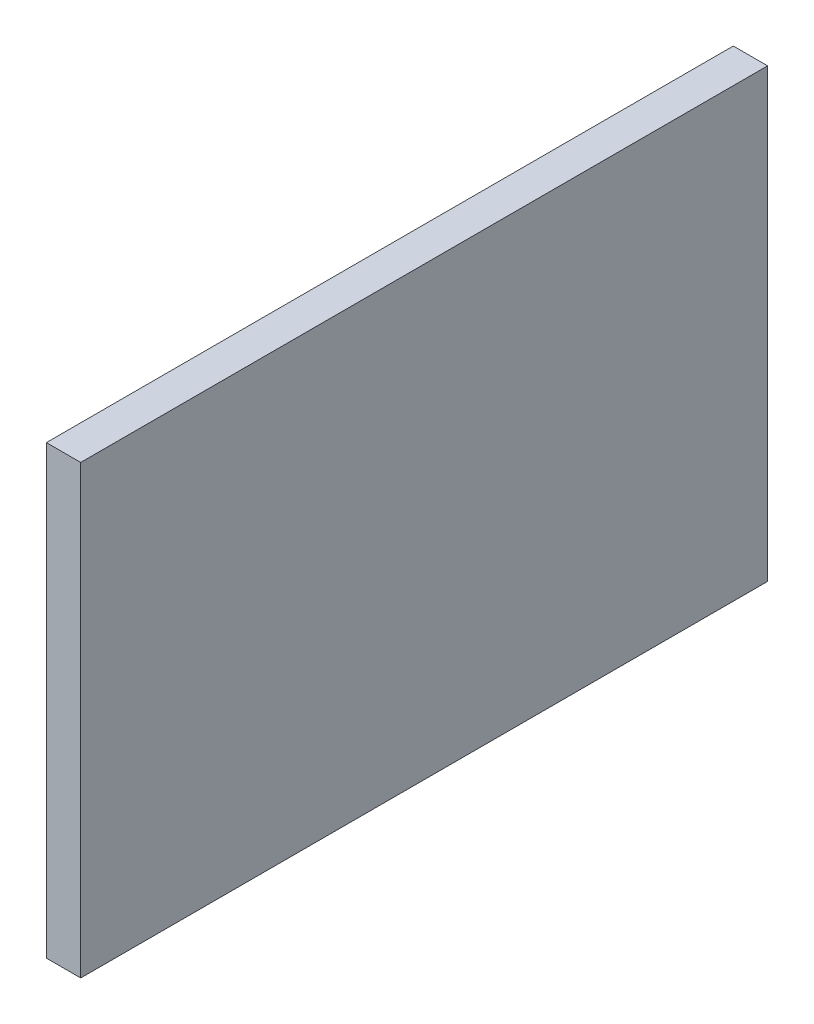
SolidWorks part; units mm, degrees
material "1060 Alloy"
ref_plane "Front Plane" through (0, 0, 0) normal (0, 0, 1) x (1, 0, 0)
ref_plane "Top Plane" through (0, 0, 0) normal (0, 1, 0) x (1, 0, 0)
ref_plane "Right Plane" through (0, 0, 0) normal (1, 0, 0) x (0, 0, -1)
sketch "Sketch1" plane through (0, 0, 0) normal (1, 0, 0) x (0, 0, -1)
  line L1 (-466.8184, 26.8007) -> (41.1816, 26.8007)
  line L2 (-466.8184, 26.8007) -> (-466.8184, -303.3993)
  line L3 (-466.8184, -303.3993) -> (41.1816, -303.3993)
  line L4 (41.1816, 26.8007) -> (41.1816, -303.3993)
  dimension "D1" = 508
  dimension "D2" = 330.2
  dimension "D3" = 41.1816
  dimension "D4" = 26.8007
extrude "Boss-Extrude1" add sketch "Sketch1" along normal blind 25.4
sketch "Sketch3" plane through (0, 0, 0) normal (-1, 0, 0) x (0, 0, 1)
  line L0 (-41.1816, 26.8007) -> (466.8184, 26.8007) construction
  line L1 (-41.1816, -303.3993) -> (-41.1816, 26.8007) construction
  circle A0 centre (9.6184, -23.9993) radius 12.7
  dimension "D1" = 25.4
  dimension "D2" = 50.8
  dimension "D3" = 50.8
extrude "Cut-Extrude2" cut sketch "Sketch3" against normal blind 6.35
